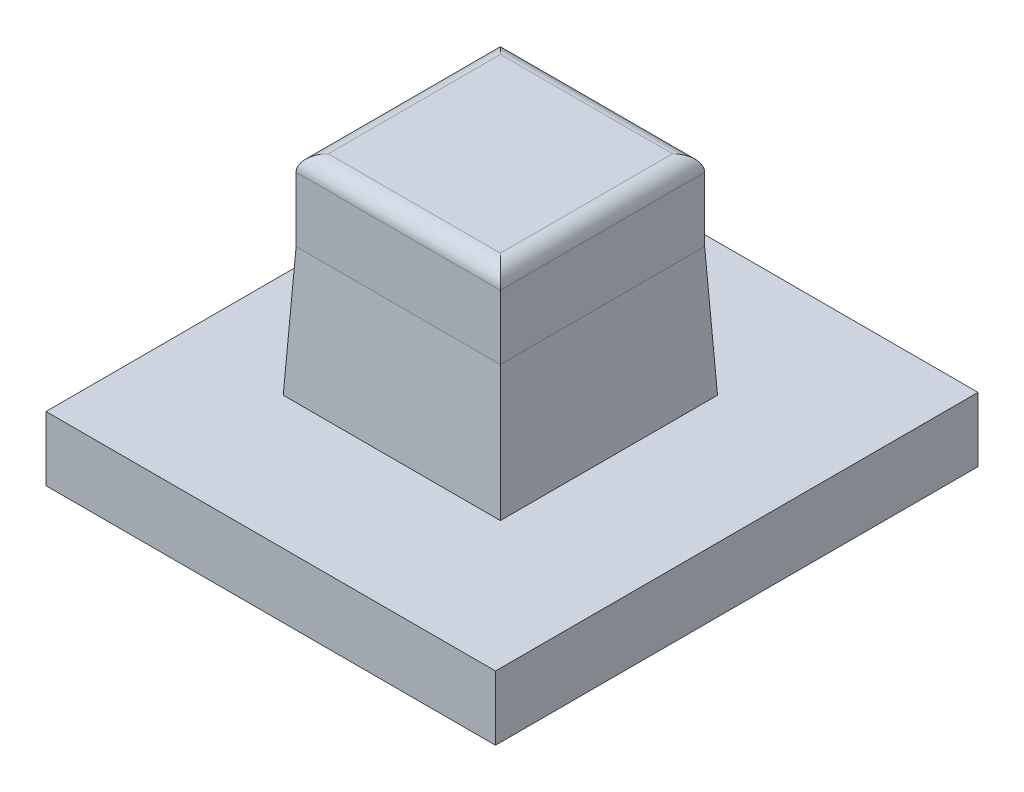
SolidWorks part; units mm, degrees
ref_plane "Front Plane" through (0, 0, 0) normal (0, 0, 1) x (1, 0, 0)
ref_plane "Top Plane" through (0, 0, 0) normal (0, 1, 0) x (1, 0, 0)
ref_plane "Right Plane" through (0, 0, 0) normal (1, 0, 0) x (0, 0, -1)
sketch "Sketch1" plane through (0, 0, 0) normal (0, 1, 0) x (1, 0, 0)
  line L0 (0, 15) -> (13.25, 15) construction
  line L1 (0, 0) -> (240, 0)
  line L2 (0, 0) -> (0, 30)
  line L3 (0, 30) -> (240, 30)
  line L4 (240, 0) -> (240, 30)
  line L5 (0, 0) -> (240, 30) construction
  line L6 (0, 30) -> (240, 0) construction
  line L7 (13.25, 15) -> (43.75, 15) construction
  line L8 (43.75, 15) -> (74.25, 15) construction
  line L9 (74.25, 15) -> (104.75, 15) construction
  line L10 (104.75, 15) -> (135.25, 15) construction
  line L11 (135.25, 15) -> (165.75, 15) construction
  line L12 (165.75, 15) -> (196.25, 15) construction
  line L14 (6.9, 21.35) -> (19.6, 21.35)
  line L15 (6.9, 21.35) -> (6.9, 8.65)
  line L16 (6.9, 8.65) -> (19.6, 8.65)
  line L17 (19.6, 21.35) -> (19.6, 8.65)
  line L18 (6.9, 21.35) -> (19.6, 8.65) construction
  line L19 (6.9, 8.65) -> (19.6, 21.35) construction
  line L23 (196.25, 15) -> (226.75, 15) construction
  line L24 (37.4, 21.35) -> (50.1, 21.35)
  line L25 (37.4, 21.35) -> (37.4, 8.65)
  line L26 (37.4, 8.65) -> (50.1, 8.65)
  line L27 (50.1, 21.35) -> (50.1, 8.65)
  line L28 (37.4, 21.35) -> (50.1, 8.65) construction
  line L29 (37.4, 8.65) -> (50.1, 21.35) construction
  line L30 (67.9, 21.35) -> (80.6, 21.35)
  line L31 (67.9, 21.35) -> (67.9, 8.65)
  line L32 (67.9, 8.65) -> (80.6, 8.65)
  line L33 (80.6, 21.35) -> (80.6, 8.65)
  line L34 (67.9, 21.35) -> (80.6, 8.65) construction
  line L35 (67.9, 8.65) -> (80.6, 21.35) construction
  line L36 (98.4, 21.35) -> (111.1, 21.35)
  line L37 (98.4, 21.35) -> (98.4, 8.65)
  line L38 (98.4, 8.65) -> (111.1, 8.65)
  line L39 (111.1, 21.35) -> (111.1, 8.65)
  line L40 (98.4, 21.35) -> (111.1, 8.65) construction
  line L41 (98.4, 8.65) -> (111.1, 21.35) construction
  line L42 (128.9, 21.35) -> (141.6, 21.35)
  line L43 (128.9, 21.35) -> (128.9, 8.65)
  line L44 (128.9, 8.65) -> (141.6, 8.65)
  line L45 (141.6, 21.35) -> (141.6, 8.65)
  line L46 (128.9, 21.35) -> (141.6, 8.65) construction
  line L47 (128.9, 8.65) -> (141.6, 21.35) construction
  line L48 (159.4, 21.35) -> (172.1, 21.35)
  line L49 (159.4, 21.35) -> (159.4, 8.65)
  line L50 (159.4, 8.65) -> (172.1, 8.65)
  line L51 (172.1, 21.35) -> (172.1, 8.65)
  line L52 (159.4, 21.35) -> (172.1, 8.65) construction
  line L53 (159.4, 8.65) -> (172.1, 21.35) construction
  line L54 (226.75, 15) -> (240, 15) construction
  line L56 (189.9, 21.35) -> (202.6, 21.35)
  line L57 (189.9, 21.35) -> (189.9, 8.65)
  line L58 (189.9, 8.65) -> (202.6, 8.65)
  line L59 (202.6, 21.35) -> (202.6, 8.65)
  line L60 (189.9, 21.35) -> (202.6, 8.65) construction
  line L61 (189.9, 8.65) -> (202.6, 21.35) construction
  line L62 (220.4, 21.35) -> (233.1, 21.35)
  line L63 (220.4, 21.35) -> (220.4, 8.65)
  line L64 (220.4, 8.65) -> (233.1, 8.65)
  line L65 (233.1, 21.35) -> (233.1, 8.65)
  line L66 (220.4, 21.35) -> (233.1, 8.65) construction
  line L67 (220.4, 8.65) -> (233.1, 21.35) construction
  point P4 (120, 15)
  point P14 (0, 15)
  point P18 (13.25, 15)
  point P24 (43.75, 15)
  point P28 (74.25, 15)
  point P33 (104.75, 15)
  point P38 (135.25, 15)
  point P43 (165.75, 15)
  point P55 (196.25, 15)
  point P56 (226.75, 15)
  dimension "D1" = 12.7
  dimension "D2" = 30.5
  dimension "D3" = 240
  dimension "D4" = 30
extrude "Boss-Extrude1" add sketch "Sketch1" along normal blind 4
sketch "Sketch2" plane through (0, 4, 0) normal (0, 1, 0) x (1, 0, 0)
  line L0 (189.9, 8.65) -> (202.6, 8.65) construction
  line L1 (6.9, 21.35) -> (19.6, 21.35)
  line L2 (6.9, 21.35) -> (6.9, 8.65)
  line L3 (6.9, 8.65) -> (19.6, 8.65)
  line L4 (19.6, 21.35) -> (19.6, 8.65)
  line L5 (6.9, 21.35) -> (19.6, 8.65) construction
  line L6 (6.9, 8.65) -> (19.6, 21.35) construction
  line L7 (37.4, 21.35) -> (50.1, 21.35)
  line L8 (37.4, 21.35) -> (37.4, 8.65)
  line L9 (37.4, 8.65) -> (50.1, 8.65)
  line L10 (50.1, 21.35) -> (50.1, 8.65)
  line L11 (37.4, 21.35) -> (50.1, 8.65) construction
  line L12 (37.4, 8.65) -> (50.1, 21.35) construction
  line L13 (67.9, 21.35) -> (80.6, 21.35)
  line L14 (67.9, 21.35) -> (67.9, 8.65)
  line L15 (67.9, 8.65) -> (80.6, 8.65)
  line L16 (80.6, 21.35) -> (80.6, 8.65)
  line L17 (67.9, 21.35) -> (80.6, 8.65) construction
  line L18 (67.9, 8.65) -> (80.6, 21.35) construction
  line L19 (98.4, 21.35) -> (111.1, 21.35)
  line L20 (98.4, 21.35) -> (98.4, 8.65)
  line L21 (98.4, 8.65) -> (111.1, 8.65)
  line L22 (111.1, 21.35) -> (111.1, 8.65)
  line L23 (98.4, 21.35) -> (111.1, 8.65) construction
  line L24 (98.4, 8.65) -> (111.1, 21.35) construction
  line L25 (128.9, 21.35) -> (141.6, 21.35)
  line L26 (128.9, 21.35) -> (128.9, 8.65)
  line L27 (128.9, 8.65) -> (141.6, 8.65)
  line L28 (141.6, 21.35) -> (141.6, 8.65)
  line L29 (128.9, 21.35) -> (141.6, 8.65) construction
  line L30 (128.9, 8.65) -> (141.6, 21.35) construction
  line L31 (159.4, 21.35) -> (172.1, 21.35)
  line L32 (159.4, 21.35) -> (159.4, 8.65)
  line L33 (159.4, 8.65) -> (172.1, 8.65)
  line L34 (172.1, 21.35) -> (172.1, 8.65)
  line L35 (159.4, 21.35) -> (172.1, 8.65) construction
  line L36 (159.4, 8.65) -> (172.1, 21.35) construction
  line L37 (189.9, 21.35) -> (202.6, 21.35)
  line L38 (189.9, 21.35) -> (189.9, 8.65)
  line L39 (189.9, 8.65) -> (202.6, 8.65)
  line L40 (202.6, 21.35) -> (202.6, 8.65)
  line L41 (189.9, 21.35) -> (202.6, 8.65) construction
  line L42 (189.9, 8.65) -> (202.6, 21.35) construction
  line L43 (220.4, 21.35) -> (233.1, 21.35)
  line L44 (220.4, 21.35) -> (220.4, 8.65)
  line L45 (220.4, 8.65) -> (233.1, 8.65)
  line L46 (233.1, 21.35) -> (233.1, 8.65)
  line L47 (220.4, 21.35) -> (233.1, 8.65) construction
  line L48 (220.4, 8.65) -> (233.1, 21.35) construction
  line L49 (202.6, 8.65) -> (202.6, 21.35) construction
  line L50 (19.6, 8.65) -> (19.6, 21.35) construction
  line L51 (6.9, 8.65) -> (19.6, 8.65) construction
  point P4 (13.25, 15)
  point P9 (43.75, 15)
  point P14 (74.25, 15)
  point P19 (104.75, 15)
  point P24 (135.25, 15)
  point P29 (165.75, 15)
  point P34 (196.25, 15)
  point P39 (226.75, 15)
extrude "Boss-Extrude2" add sketch "Sketch2" along normal blind 13 and the other way up to surface (4 mm away) other way up to face at (120, 0, -15)
sketch "Sketch3" plane through (0, 4, 0) normal (0, 1, 0) x (1, 0, 0)
  line L1 (27.9456, 58.4021) -> (245.0726, 58.4021)
  line L2 (27.9456, 58.4021) -> (27.9456, -37.0358)
  line L3 (27.9456, -37.0358) -> (245.0726, -37.0358)
  line L4 (245.0726, 58.4021) -> (245.0726, -37.0358)
  line L5 (27.9456, 58.4021) -> (245.0726, -37.0358) construction
  line L6 (27.9456, -37.0358) -> (245.0726, 58.4021) construction
  point P4 (136.5091, 10.6831)
extrude "Cut-Extrude1" cut sketch "Sketch3" against normal through all both and the other way through all
fillet "Fillet1" radius 1 4 edges at (13.25, 17, -21.35) (19.6, 17, -15) (13.25, 17, -8.65) (6.9, 17, -15)
chamfer "Chamfer1" distance 0.4 distance2 8 4 edges at (19.6, 4, -15) (13.25, 4, -21.35) (6.9, 4, -15) (13.25, 4, -8.65)
